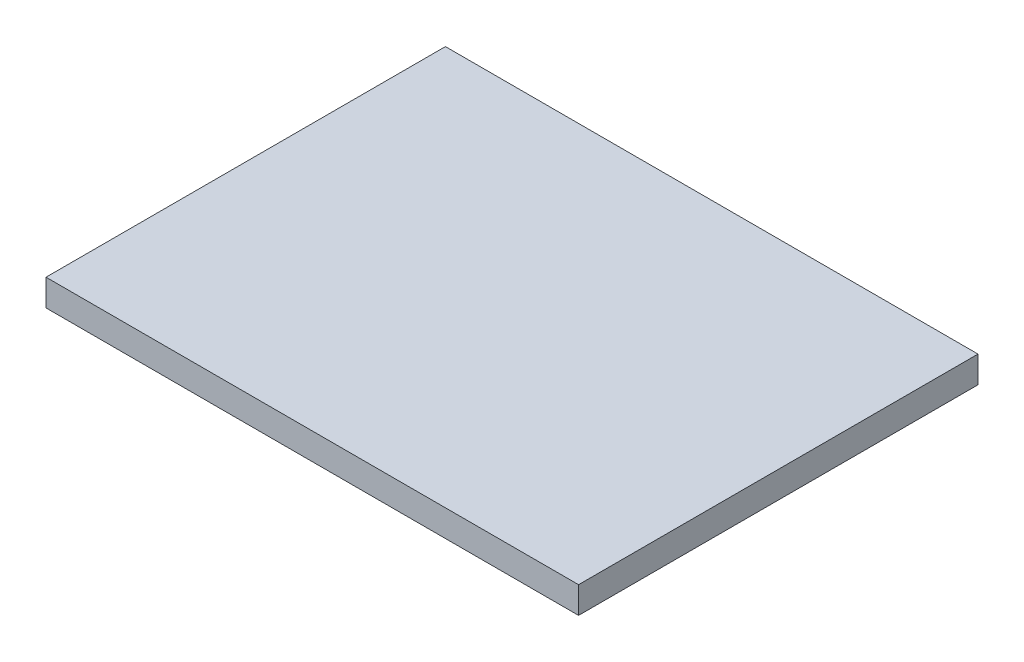
SolidWorks part; units mm, degrees
ref_plane "Piano frontale" through (0, 0, 0) normal (0, 0, 1) x (1, 0, 0)
ref_plane "Piano superiore" through (0, 0, 0) normal (0, 1, 0) x (1, 0, 0)
ref_plane "Piano destro" through (0, 0, 0) normal (1, 0, 0) x (0, 0, -1)
sketch "Schizzo2" plane through (0, 0, 0) normal (0, 1, 0) x (1, 0, 0)
  line L1 (100, -75) -> (-100, -75)
  line L2 (100, -75) -> (100, 75)
  line L3 (100, 75) -> (-100, 75)
  line L4 (-100, -75) -> (-100, 75)
  line L5 (100, -75) -> (-100, 75) construction
  line L6 (100, 75) -> (-100, -75) construction
  point P0 (0, 0)
  dimension "D1" = 150
  dimension "D2" = 200
extrude "Estrusione-Estrusione1" add sketch "Schizzo2" along normal blind 10
